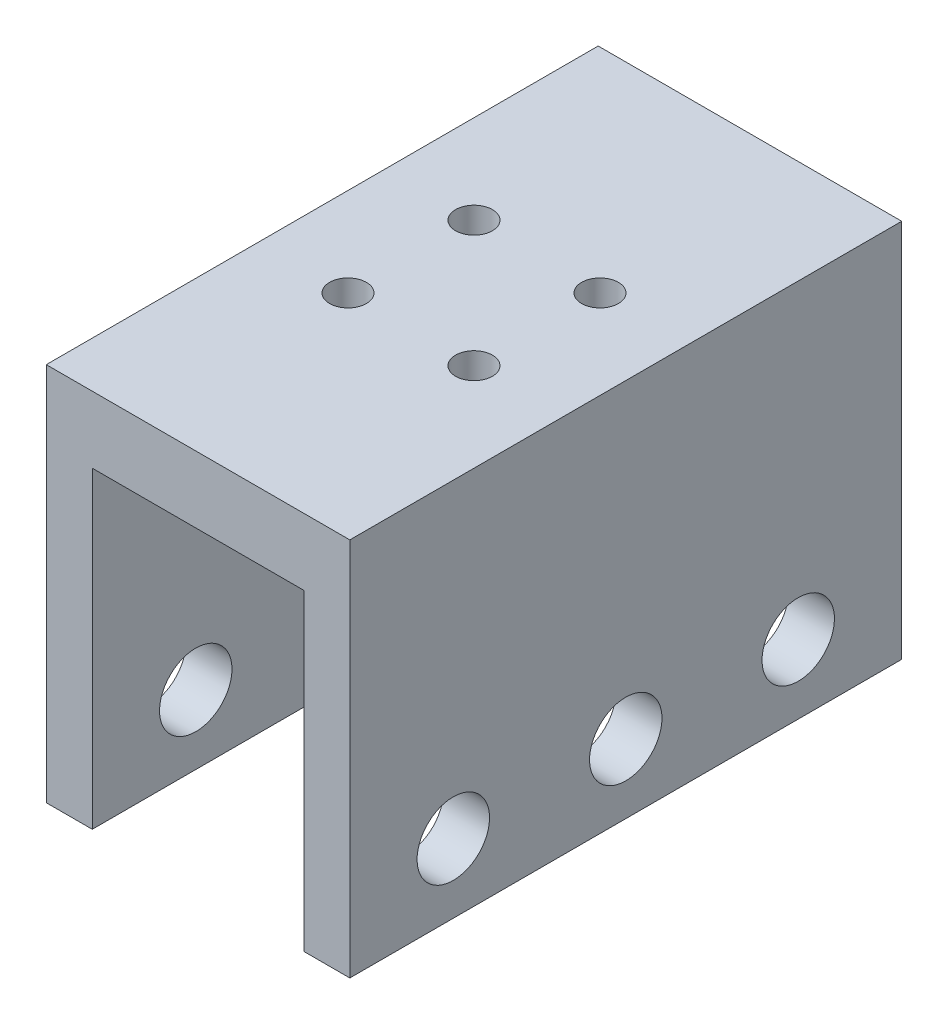
SolidWorks part; units mm, degrees
ref_plane "前基準面" through (0, 0, 0) normal (0, 0, 1) x (1, 0, 0)
ref_plane "上基準面" through (0, 0, 0) normal (0, 1, 0) x (1, 0, 0)
ref_plane "右基準面" through (0, 0, 0) normal (1, 0, 0) x (0, 0, -1)
sketch "草圖1" plane through (0, 0, 0) normal (0, 0, 1) x (1, 0, 0)
  line L0 (0, 0) -> (0, 33)
  line L5 (0, 33) -> (26.4, 33)
  line L6 (26.4, 33) -> (26.4, 0)
  line L12 (26.4, 0) -> (22.4, 0)
  line L13 (22.4, 0) -> (22.4, 27.2)
  line L14 (22.4, 27.2) -> (4, 27.2)
  line L15 (4, 27.2) -> (4, 0)
  line L16 (4, 0) -> (0, 0)
  point P9 (29.1426, 0)
  point P10 (21.738, 0)
  dimension "D1" = 27.2
  dimension "D2" = 33
  dimension "D3" = 4
  dimension "D4" = 4
  dimension "D5" = 26.4
extrude "填料-伸長1" add sketch "草圖1" along normal mid plane 48
sketch "草圖2" plane through (0, 27.2, 0) normal (0, -1, 0) x (1, 0, 0)
  line L0 (13.2, 0) -> (20.3284, 0) construction
  line L2 (13.2, 24) -> (13.2, 22.7227) construction
  line L3 (4, 24) -> (22.4, 24) construction
  circle A0 centre (13.2, 0) radius 10 construction
  circle A1 centre (7.7199, 5.4801) radius 1.6
  circle A2 centre (18.6801, 5.4801) radius 1.6
  circle A3 centre (18.6801, -5.4801) radius 1.6
  circle A4 centre (7.7199, -5.4801) radius 1.6
  point P4 (10.6061, -0.6015)
  point P6 (23.665, 0)
  point P13 (13.2, 0)
  dimension "D1" = 20
  dimension "D2" = 3.2
  dimension "D3" = 7.75
  dimension "D4" = 4
extrude "除料-伸長1" cut sketch "草圖2" against normal through all
sketch "草圖3" plane through (26.4, 0, 0) normal (1, 0, 0) x (0, 0, -1)
  line L0 (-24, 0) -> (24, 0) construction
  line L1 (0, 0) -> (0, 16.3853) construction
  circle A0 centre (0, 6) radius 3.15
  circle A1 centre (15, 6) radius 3.15
  circle A2 centre (-15, 6) radius 3.15
  point P11 (0, 0)
  point P12 (0, 11.3968)
  dimension "D1" = 6.3
  dimension "D2" = 6
  dimension "D3" = 15
extrude "除料-伸長2" cut sketch "草圖3" against normal up to surface (26.4 mm away) up to face at (0, 16.5, 0)
